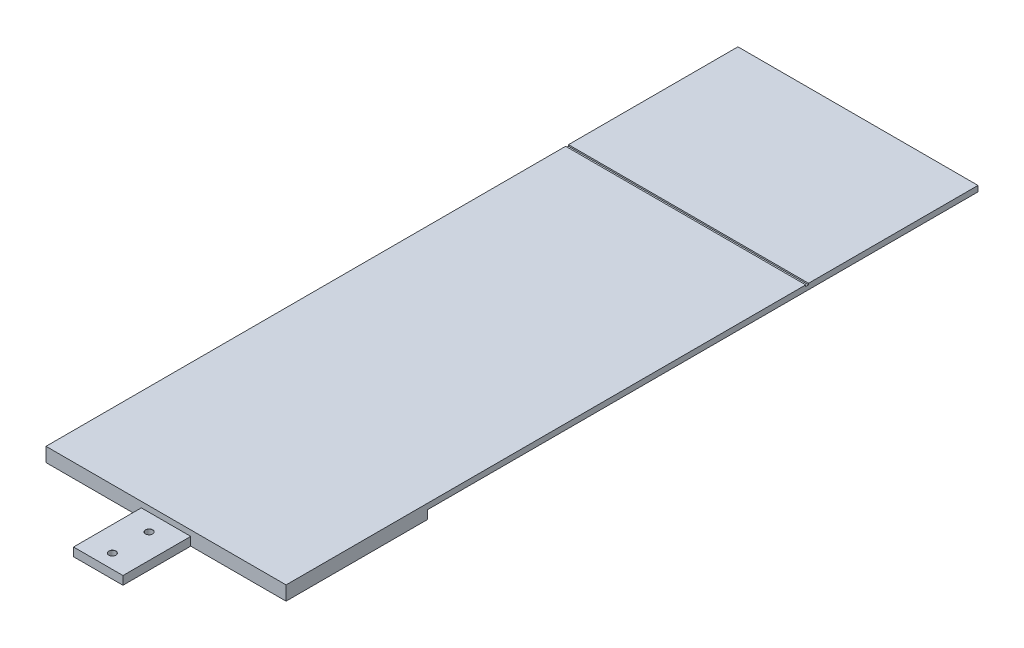
SolidWorks part; units mm, degrees
ref_plane "Front Plane" through (0, 0, 0) normal (0, 0, 1) x (1, 0, 0)
ref_plane "Top Plane" through (0, 0, 0) normal (0, 1, 0) x (1, 0, 0)
ref_plane "Right Plane" through (0, 0, 0) normal (1, 0, 0) x (0, 0, -1)
sketch "Sketch2" plane through (0, 0, 0) normal (0, 1, 0) x (1, 0, 0)
  line L1 (42.5, 0) -> (42.5, 50)
  line L2 (42.5, 50) -> (22.5, 50)
  line L3 (22.5, 50) -> (8.75, 26.1843)
  line L4 (8.75, 26.1843) -> (-8.75, 26.1843)
  line L5 (-8.75, 26.1843) -> (-22.5, 50)
  line L6 (-22.5, 50) -> (-42.5, 50)
  line L7 (-42.5, 50) -> (-42.5, 0)
  line L9 (-42.5, 0) -> (42.5, 0)
  point P0 (0, 26.1843)
  point P3 (0, 0)
  point P11 (32.5, 50)
  point P13 (-32.5, 50)
  dimension "D1" = 17.5
  dimension "D2" = 85
  dimension "D3" = 50
  dimension "D4" = 60
  dimension "D5" = 60
  dimension "D6" = 20
extrude "Boss-Extrude1" add sketch "Sketch2" along normal blind 3
sketch "Sketch3" plane through (0, 0, -26.1843) normal (0, 0, -1) x (-1, 0, 0)
  line L6 (-8.75, 0) -> (8.75, 0)
  line L7 (-8.75, 0) -> (-8.75, 1)
  line L8 (-8.75, 1) -> (8.75, 1)
  line L9 (8.75, 0) -> (8.75, 1)
  point P5 (0, 0)
  dimension "D1" = 17.5
  dimension "D2" = 1
extrude "Cut-Extrude1" [suppressed] cut sketch "Sketch3" against normal through all
sketch "Sketch10" plane through (0, 3, 0) normal (0, 1, 0) x (1, 0, 0)
  line L0 (-8.75, 0) -> (-8.75, -24)
  line L1 (-42.5, 0) -> (42.5, 0) construction
  line L2 (-8.75, -24) -> (8.75, -24)
  line L3 (8.75, -24) -> (8.75, 0)
  line L4 (8.75, 0) -> (-8.75, 0)
  point P4 (0, 0)
  dimension "D1" = 17.5
  dimension "D2" = 24
extrude "Boss-Extrude2" add sketch "Sketch10" against normal up to surface (3 mm away) up to face at (0, 0, -31.5461)
hole_wizard "Ø2.5 (2.5) Diameter Hole1" positions "Sketch4" profile "Sketch5" hole size "Ø2.5" standard "ANSI Metric"
sketch "Sketch4" plane through (0, 3, 0) normal (0, 1, 0) x (1, 0, 0)
  line L4 (-8.75, -24) -> (8.75, -24) construction
  point P0 (0, -19)
  point P2 (0, -6)
  dimension "D1" = 13
  dimension "D2" = 5
  dimension "D3" = 8.75
sketch "Sketch5" plane through (0, 3, 19) normal (1, 0, 0) x (0, 0, 1)
  line L0 (0, 0) -> (0, 7.1011)
  line L1 (0, 7.1011) -> (1.25, 6.35)
  line L2 (1.25, 6.35) -> (1.25, 0.025)
  line L3 (1.25, 0.025) -> (1.275, 0)
  line L5 (1.275, 0) -> (0, 0)
  line L6 (-1.25, 0.025) -> (-1.275, 0) construction
  line L10 (0, 7.1011) -> (-1.25, 6.35) construction
  line L11 (0, -6.35) -> (0, 107.95) construction
  dimension "Hole Dia." = 2.5
  dimension "Hole Depth" = 6.35
  dimension "Near C'Sink Dia." = 2.55
  dimension "Near C'Sink Angle" = 90
  dimension "Drill Angle" = 118
hole_wizard "M5x0.8 Tapped Hole1" [suppressed] positions "Sketch6" profile "Sketch7" tap size "M5x0.8" standard "ANSI Metric"
sketch "Sketch6" plane through (0, 3, 0) normal (0, 1, 0) x (1, 0, 0)
  line L1 (-22.5, 50) -> (-42.5, 50) construction
  line L2 (42.5, 50) -> (22.5, 50) construction
  line L3 (42.5, 0) -> (42.5, 50) construction
  line L4 (-42.5, 50) -> (-42.5, 0) construction
  line L5 (-42.5, 0) -> (-8.75, 0) construction
  point P0 (-36.5, 40)
  point P2 (36.5, 40)
  point P18 (-36.5, 10)
  point P20 (36.5, 10)
  dimension "D1" = 6
  dimension "D2" = 10
  dimension "D3" = 10
  dimension "D4" = 6
  dimension "D5" = 10
  dimension "D6" = 10
sketch "Sketch7" plane through (-36.5, 3, -40) normal (1, 0, 0) x (0, 0, 1)
  line L0 (0, 0) -> (0, 13.6618)
  line L1 (0, 13.6618) -> (2.1, 12.4)
  line L2 (2.1, 12.4) -> (2.1, 0.425)
  line L3 (2.1, 0.425) -> (2.525, 0)
  line L5 (2.525, 0) -> (0, 0)
  line L6 (-2.1, 0.425) -> (-2.525, 0) construction
  line L10 (0, 13.6618) -> (-2.1, 12.4) construction
  line L11 (0, -6.35) -> (0, 107.95) construction
  dimension "Tap Drill Dia." = 4.2
  dimension "Tap Drill Depth" = 12.4
  dimension "Near C'Sink Dia." = 5.05
  dimension "Near C'Sink Angle" = 90
  dimension "Drill Angle" = 118
cosmetic thread "Hole Thread3" [suppressed] parameters "D1"=10, "D2"=5
cosmetic thread "Hole Thread4" [suppressed] parameters "D1"=10, "D2"=5
cosmetic thread "Hole Thread5" [suppressed] parameters "D1"=10, "D2"=5
cosmetic thread "Hole Thread6" [suppressed] parameters "D1"=10, "D2"=5
sketch "Sketch8" plane through (0, 0, -26.1843) normal (0, 0, -1) x (-1, 0, 0)
  line L5 (-8.75, 3) -> (-8.75, 0) construction
  line L6 (-13, 0) -> (-8.75, 0)
  line L7 (-13, 0) -> (-13, 1.3)
  line L8 (-13, 1.3) -> (-8.75, 1.3)
  line L9 (-8.75, 0) -> (-8.75, 1.3)
  line L10 (0, 0) -> (0, 12.6228) construction
  line L11 (8.75, 0) -> (8.75, 1.3)
  line L12 (13, 1.3) -> (8.75, 1.3)
  line L13 (13, 0) -> (13, 1.3)
  line L14 (13, 0) -> (8.75, 0)
  line L15 (-22.5, 0) -> (-8.75, 0) construction
  dimension "D1" = 4.25
  dimension "D2" = 1.3
extrude "Cut-Extrude2" [suppressed] cut sketch "Sketch8" against normal through all both and the other way through all
sketch "Sketch9" plane through (0, 0, 0) normal (0, -1, 0) x (1, 0, 0)
  line L0 (-32, -50) -> (-25, -26.1843)
  line L1 (-22.5, -50) -> (-42.5, -50) construction
  line L3 (25, -26.1843) -> (32, -50)
  line L4 (42.5, -50) -> (22.5, -50) construction
  line L5 (32, -50) -> (-32, -50)
  line L6 (-25, -26.1843) -> (25, -26.1843)
  line L7 (8.75, -26.1843) -> (-8.75, -26.1843) construction
  point P8 (0, -50)
  point P12 (0, -26.1843)
  dimension "D1" = 64
  dimension "D2" = 50
extrude "Cut-Extrude3" cut sketch "Sketch9" against normal through all
fillet "Fillet1" [suppressed] radius 3
fillet "Fillet2" [suppressed] radius 1
sketch "Sketch11" plane through (0, 3, 0) normal (0, 1, 0) x (1, 0, 0)
  line L1 (42.5, 0) -> (-42.5, 0)
  line L2 (42.5, 0) -> (42.5, 245)
  line L3 (42.5, 245) -> (-42.5, 245)
  line L4 (-42.5, 0) -> (-42.5, 245)
  point P4 (0, 0)
  dimension "D1" = 245
  dimension "D2" = 85
extrude "Boss-Extrude3" add sketch "Sketch11" along normal blind 2
sketch "Sketch12" plane through (-42.5, 0, 0) normal (-1, 0, 0) x (0, 0, 1)
  line L0 (-245, 5) -> (0, 5) construction
  line L1 (-185, 5) -> (-184, 5)
  line L2 (-185, 5) -> (-185, 4.5)
  line L3 (-185, 4.5) -> (-184, 4.5)
  line L4 (-184, 5) -> (-184, 4.5)
  line L5 (-245, 5) -> (-245, 3) construction
  dimension "D1" = 0.5
  dimension "D2" = 1
  dimension "D3" = 60
extrude "Cut-Extrude4" cut sketch "Sketch12" against normal through all both and the other way through all
